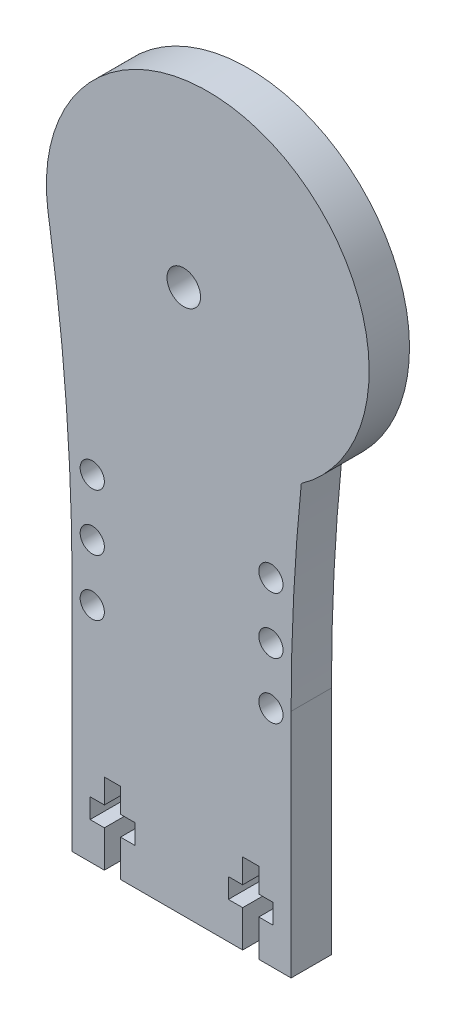
SolidWorks part; units mm, degrees
material "Acrílico (médio-alto impacto)"
ref_plane "Plano frontal" through (0, 0, 0) normal (0, 0, 1) x (1, 0, 0)
ref_plane "Plano superior" through (0, 0, 0) normal (0, 1, 0) x (1, 0, 0)
ref_plane "Plano direito" through (0, 0, 0) normal (1, 0, 0) x (0, 0, -1)
sketch "Esboço1" plane through (0, 0, 0) normal (0, 0, 1) x (1, 0, 0)
  line L0 (13.5691, 56.3389) -> (13.5691, 27.7156)
  line L1 (-13.5691, 56.3389) -> (-13.5691, 27.7156)
  line L2 (-16.3694, 93.6521) -> (-16.5765, 95.0244)
  arc A0 (13.5691, 27.7156) -> (-13.5691, 27.7156) centre (0, 38.1348) cw
  arc A1 (13.5691, 56.3389) -> (14.8299, 81.415) centre (263.5691, 56.3389) cw
  arc A2 (-13.5691, 56.3389) -> (-16.3694, 93.6521) centre (-263.5691, 56.3389) ccw
  arc A3 (14.8299, 81.415) -> (-16.4879, 94.4373) centre (3.2416, 97.7156) ccw
  dimension "D1" = 70
  dimension "D5" = 250
  dimension "D6" = 250
  dimension "D2" = 40
  dimension "D3" = 70
extrude "Ressalto-extrusão1" add sketch "Esboço1" along normal blind 5
sketch "Esboço4" plane through (0, 0, 5) normal (0, 0, 1) x (1, 0, 0)
  circle A0 centre (-4.6155, 109.78) radius 1.5
  circle A1 centre (5.3845, 109.78) radius 1.5
  circle A2 centre (-4.6155, 60) radius 1.5
  circle A3 centre (5.3845, 60) radius 1.5
  arc A4 (14.8299, 81.415) -> (13.5691, 56.3389) centre (263.5691, 56.3389) ccw construction
  point P11 (13.8845, 68.8928)
  dimension "D1" = 49.78
  dimension "D2" = 49.78
  dimension "D3" = 10
  dimension "D4" = 10
  dimension "D5" = 3
  dimension "D6" = 3
  dimension "D7" = 3
  dimension "D8" = 3
  dimension "D9" = 8.5
  dimension "D12" = 10
sketch "Esboço5" plane through (0, 0, 5) normal (0, 0, 1) x (1, 0, 0)
  line L1 (-9.6324, 105.19) -> (10.1676, 105.19)
  line L2 (-9.6324, 105.19) -> (-9.6324, 64.59)
  line L3 (-9.6324, 64.59) -> (10.1676, 64.59)
  line L4 (10.1676, 105.19) -> (10.1676, 64.59)
sketch "Esboço7" plane through (0, 0, 0) normal (0, 0, -1) x (-1, 0, 0)
  line L0 (-10.1676, 105.19) -> (-10.1676, 64.59) construction
  circle A0 centre (-0.2676, 95.19) radius 2.0767
  circle A1 centre (-5.3845, 109.78) radius 1.5 construction
  dimension "D1" = 14.59
  dimension "D2" = 9.9
extrude "Corte-extrusão5" cut sketch "Esboço7" against normal through all
sketch "Esboço8" plane through (0, 0, 5) normal (0, 0, 1) x (1, 0, 0)
  line L1 (13.5691, 27.7156) -> (-19.3723, 27.7156)
  line L2 (13.5691, 27.7156) -> (13.5691, 20.012)
  line L3 (13.5691, 20.012) -> (-19.3723, 20.012)
  line L4 (-19.3723, 27.7156) -> (-19.3723, 20.012)
extrude "Corte-extrusão6" cut sketch "Esboço8" against normal through all
sketch "Esboço9" plane through (0, 0, 0) normal (0, 0, -1) x (-1, 0, 0)
  circle A0 centre (11.0724, 69.41) radius 1.5
  circle A1 centre (11.0724, 62.41) radius 1.5
  circle A2 centre (11.0724, 55.41) radius 1.5
  circle A3 centre (-11.0676, 69.41) radius 1.5
  circle A4 centre (-11.0676, 62.41) radius 1.5
  circle A5 centre (-11.0676, 55.41) radius 1.5
  circle A6 centre (-0.2676, 95.19) radius 2.0767 construction
  dimension "D1" = 11.34
  dimension "D2" = 25.78
  dimension "D3" = 7
  dimension "D4" = 7
  dimension "D5" = 11.34
  dimension "D6" = 11.34
  dimension "D7" = 3
  dimension "D8" = 3
  dimension "D9" = 3
  dimension "D10" = 25.78
  dimension "D12" = 7
  dimension "D13" = 3
  dimension "D14" = 3
  dimension "D15" = 3
  dimension "D16" = 22.14
  dimension "D17" = 22.14
  dimension "D18" = 22.14
  dimension "D11" = 7
extrude "Corte-extrusão7" cut sketch "Esboço9" against normal through all
sketch "Esboço10" plane through (0, 0, 0) normal (0, 0, -1) x (-1, 0, 0)
  line L0 (-13.5691, 27.7156) -> (13.5691, 27.7156) construction
  line L1 (9.5691, 27.7156) -> (7.5691, 27.7156)
  line L2 (9.5691, 27.7156) -> (9.5691, 32.2656)
  line L3 (9.5691, 37.7156) -> (7.5691, 37.7156)
  line L4 (7.5691, 27.7156) -> (7.5691, 32.2656)
  line L5 (13.5691, 56.3389) -> (13.5691, 27.7156) construction
  line L6 (-7.5691, 27.7156) -> (-9.5691, 27.7156)
  line L7 (-7.5691, 27.7156) -> (-7.5691, 32.2656)
  line L8 (-7.5691, 37.7156) -> (-9.5691, 37.7156)
  line L9 (-9.5691, 27.7156) -> (-9.5691, 32.2656)
  line L10 (-13.5691, 56.3389) -> (-13.5691, 27.7156) construction
  line L11 (7.5691, 32.2656) -> (5.7991, 32.2656)
  line L12 (11.3391, 32.2656) -> (9.5691, 32.2656)
  line L13 (11.3391, 32.2656) -> (11.3391, 34.7156)
  line L14 (11.3391, 34.7156) -> (5.7991, 34.7156)
  line L15 (5.7991, 32.2656) -> (5.7991, 34.7156)
  line L16 (-5.7991, 32.2656) -> (-7.5691, 32.2656)
  line L17 (-5.7991, 32.2656) -> (-5.7991, 34.7156)
  line L18 (-5.7991, 34.7156) -> (-7.5691, 34.7156)
  line L19 (-11.3391, 32.2656) -> (-11.3391, 34.7156)
  line L20 (9.5691, 34.7156) -> (9.5691, 37.7156)
  line L21 (7.5691, 34.7156) -> (7.5691, 37.7156)
  line L22 (-9.5691, 32.2656) -> (-11.3391, 32.2656)
  line L23 (-9.5691, 34.7156) -> (-11.3391, 34.7156)
  line L24 (-7.5691, 34.7156) -> (-7.5691, 37.7156)
  line L25 (-9.5691, 34.7156) -> (-9.5691, 37.7156)
  line M23 (-13.5691, 27.7156) -> (13.5691, 27.7156)
  dimension "D1" = 2
  dimension "D2" = 4
  dimension "D3" = 4
  dimension "D4" = 2
  dimension "D5" = 4.55
  dimension "D6" = 4.55
  dimension "D7" = 2.45
  dimension "D8" = 2.45
  dimension "D9" = 3
  dimension "D10" = 3
  dimension "D11" = 1.77
  dimension "D12" = 1.77
  dimension "D13" = 1.77
  dimension "D14" = 1.77
extrude "Corte-extrusão8" cut sketch "Esboço10" against normal through all contours L15 L11 L4 L2 L12 L13 L14 M23 | L21 L14 L20 L3 | L25 L23 L19 L22 L9 L7 L16 L17 L18 L24 L8 M23
